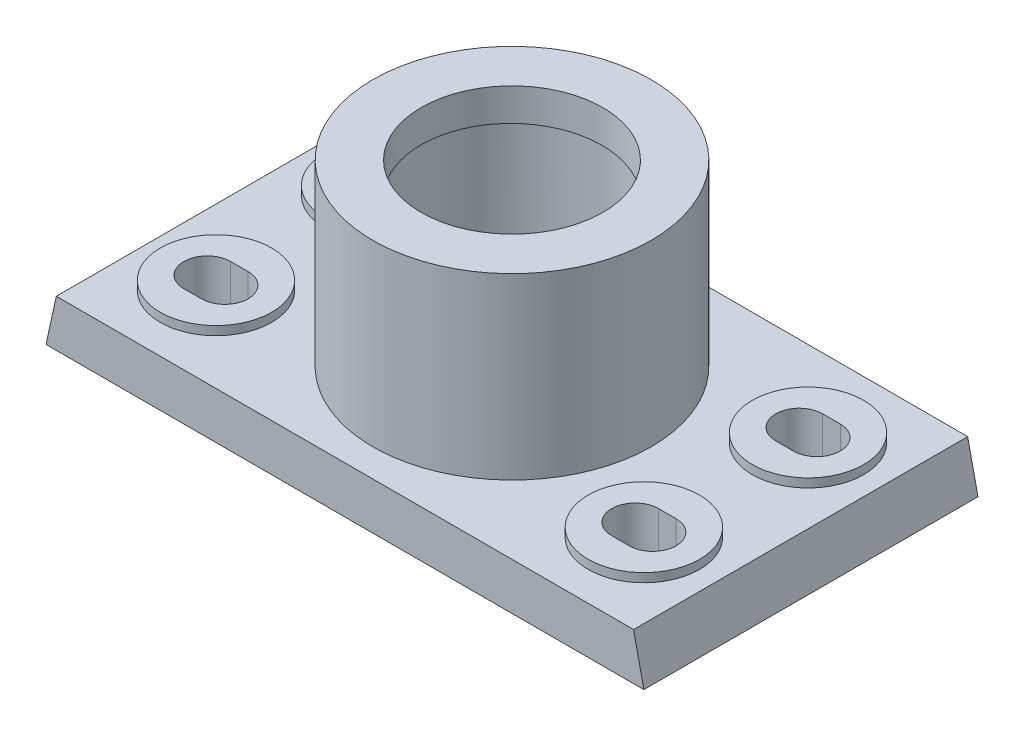
SolidWorks part; units mm, degrees
ref_plane "Front Plane" through (0, 0, 0) normal (0, 0, 1) x (1, 0, 0)
ref_plane "Top Plane" through (0, 0, 0) normal (0, 1, 0) x (1, 0, 0)
ref_plane "Right Plane" through (0, 0, 0) normal (1, 0, 0) x (0, 0, -1)
sketch "Sketch1" plane through (0, 0, 0) normal (0, 0, 1) x (1, 0, 0)
  line L0 (-177.7806, 0) -> (226.7022, 0) construction
  line L1 (0, 104.0784) -> (0, -132.2163) construction
  line L2 (102, 0) -> (-102, 0)
  line L3 (-102, 0) -> (-98.4828, 16)
  line L4 (-98.4828, 16) -> (98.4828, 16)
  line L5 (98.4828, 16) -> (102, 0)
  point P8 (0, 0)
  dimension "D1" = 204
  dimension "D2" = 16
  dimension "D3" = 3.5172
extrude "Boss-Extrude1" add sketch "Sketch1" along normal mid plane 114
sketch "Sketch2" plane through (0, 0, 0) normal (0, -1, 0) x (1, 0, 0)
  line L0 (-102, 57) -> (-102, -57) construction
  line L1 (-92, 47) -> (-6.5, 47)
  line L2 (-92, 47) -> (-92, -47)
  line L3 (-92, -47) -> (-6.5, -47)
  line L4 (-6.5, 47) -> (-6.5, -47)
  line L5 (-102, 57) -> (102, 57) construction
  line L6 (-102, -57) -> (102, -57) construction
  dimension "D1" = 10
  dimension "D2" = 10
  dimension "D3" = 10
  dimension "D4" = 85.5
extrude "Cut-Extrude1" cut sketch "Sketch2" against normal blind 3
mirror "Mirror1" about plane through (0, 0, 0) normal (1, 0, 0) of "Cut-Extrude1"
sketch "Sketch5" plane through (0, 16, 0) normal (0, 1, 0) x (1, 0, 0)
  line L0 (98.4828, 57) -> (-98.4828, 57) construction
  line L1 (-102, -57) -> (-102, 57) construction
  line L2 (98.4828, -57) -> (-98.4828, -57) construction
  circle A0 centre (-73, 28) radius 19
  circle A1 centre (-73, -28) radius 19
  dimension "D1" = 38
  dimension "D2" = 29
  dimension "D3" = 29
  dimension "D4" = 29
  dimension "D5" = 29
extrude "Boss-Extrude4" add sketch "Sketch5" along normal blind 3
sketch "Sketch6" plane through (0, 19, 0) normal (0, 1, 0) x (1, 0, 0)
  line L0 (-76, 28) -> (-70, 28) construction
  line L1 (-76, 36) -> (-70, 36)
  line L2 (-76, 20) -> (-70, 20)
  line L3 (-76, -28) -> (-70, -28) construction
  line L4 (-76, -20) -> (-70, -20)
  line L5 (-76, -36) -> (-70, -36)
  arc A0 (-76, 36) -> (-76, 20) centre (-76, 28) ccw
  arc A1 (-70, 20) -> (-70, 36) centre (-70, 28) ccw
  arc A2 (-76, -20) -> (-76, -36) centre (-76, -28) ccw
  arc A3 (-70, -36) -> (-70, -20) centre (-70, -28) ccw
  point P2 (-73, 28)
  point P10 (-73, -28)
extrude "Cut-Extrude3" cut sketch "Sketch6" against normal through all
mirror "Mirror2" about plane through (0, 0, 0) normal (1, 0, 0) of "Boss-Extrude4", "Cut-Extrude3"
sketch "Sketch7" plane through (0, 16, 0) normal (0, 1, 0) x (1, 0, 0)
  circle A0 centre (0, 0) radius 31
  circle A1 centre (0, 0) radius 47.5
  dimension "D1" = 62
  dimension "D2" = 95
extrude "Boss-Extrude5" add sketch "Sketch7" along normal blind 61
sketch "Sketch12" plane through (0, 0, 0) normal (0, 0, 1) x (1, 0, 0)
  line L0 (47.5, 77) -> (-47.5, 77) construction
  line L1 (-32.5, 66) -> (-29.5, 66)
  line L2 (-32.5, 66) -> (-32.5, 29)
  line L3 (-32.5, 29) -> (-29.5, 29)
  line L4 (-29.5, 66) -> (-29.5, 29)
  line L5 (0, 0) -> (1.1209, 107.4391) construction
  dimension "D1" = 11
  dimension "D2" = 3
  dimension "D3" = 32.5
  dimension "D4" = 37
revolve "Cut-Revolve6" cut sketch "Sketch12" angle 360 about L5
sketch "Sketch17" plane through (0, 16, 0) normal (0, 1, 0) x (1, 0, 0)
  circle A0 centre (-23.5, 2.2028) radius 1.5
  dimension "D1" = 3
  dimension "D2" = 23.5
extrude "Cut-Extrude4" cut sketch "Sketch17" against normal blind 10
